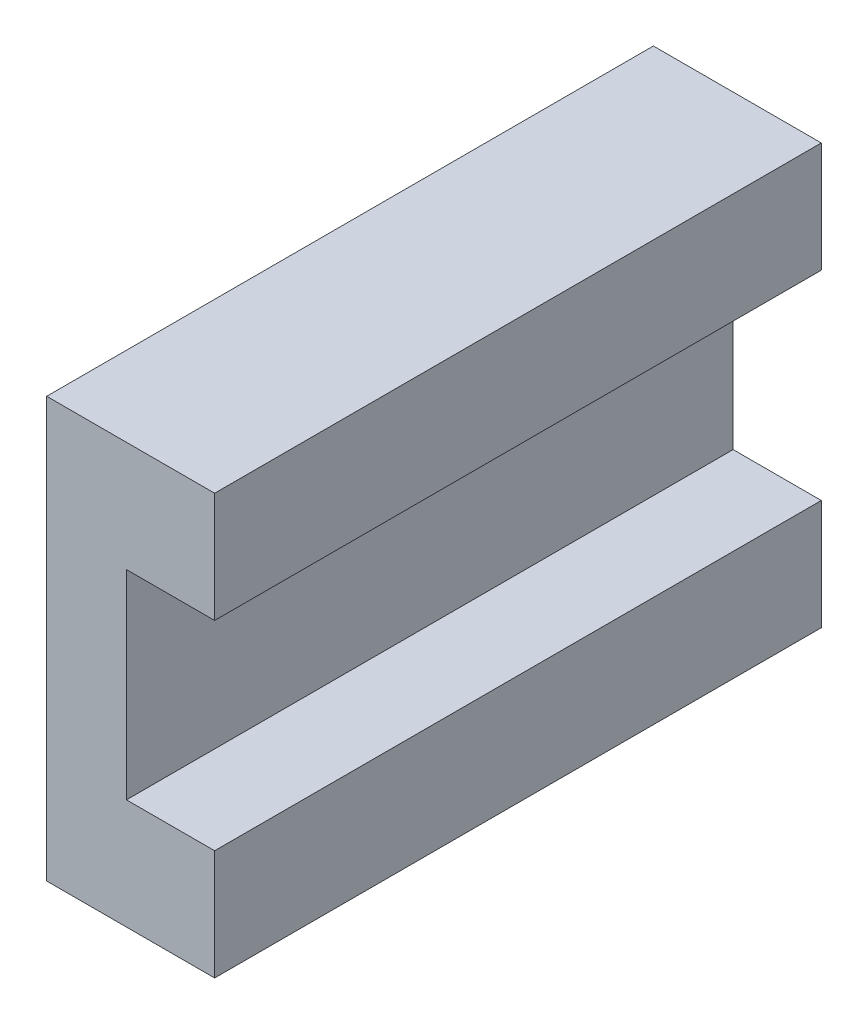
SolidWorks part; units mm, degrees
ref_plane "Front Plane" through (0, 0, 0) normal (0, 0, 1) x (1, 0, 0)
ref_plane "Top Plane" through (0, 0, 0) normal (0, 1, 0) x (1, 0, 0)
ref_plane "Right Plane" through (0, 0, 0) normal (1, 0, 0) x (0, 0, -1)
sketch "Sketch1" plane through (0, 0, 0) normal (0, 0, 1) x (1, 0, 0)
  line L1 (3.25, 4.5) -> (-3.25, 4.5)
  line L2 (3.25, 4.5) -> (3.25, -4.5)
  line L3 (3.25, -4.5) -> (-3.25, -4.5)
  line L4 (-3.25, 4.5) -> (-3.25, -4.5)
  line L5 (0, -4.5) -> (0, 4.5) construction
  line L6 (3.25, 0) -> (-3.25, 0) construction
  point P0 (0, 0)
  dimension "D1" = 6.5
  dimension "D2" = 9
extrude "Boss-Extrude1" add sketch "Sketch1" along normal mid plane 300
sketch "Sketch2" plane through (0, 0, 0) normal (0, 0, 1) x (1, 0, 0)
  line L0 (3.25, -4.5) -> (3.25, 4.5) construction
  line L1 (0.75, 10) -> (-7.25, 10)
  line L2 (0.75, 10) -> (0.75, -10)
  line L3 (0.75, -10) -> (-7.25, -10)
  line L4 (-7.25, 10) -> (-7.25, -10)
  line L5 (-3.25, -10) -> (-3.25, 10) construction
  line L6 (0.75, 0) -> (-7.25, 0) construction
  line L7 (0.75, 4.75) -> (-3.45, 4.75)
  line L8 (0.75, 4.75) -> (0.75, -4.75)
  line L9 (0.75, -4.75) -> (-3.45, -4.75)
  line L10 (-3.45, 4.75) -> (-3.45, -4.75)
  line L11 (-1.35, -4.75) -> (-1.35, 4.75) construction
  line L12 (0.75, 0) -> (-3.45, 0) construction
  line L13 (-3.25, 4.5) -> (-3.25, -4.5) construction
  point P144 (-1.35, 0)
  point P340 (-3.25, 0)
  dimension "D1" = 8
  dimension "D2" = 2.5
  dimension "D3" = 0.2
  dimension "D4" = 9.5
  dimension "D5" = 20
extrude "Boss-Extrude2" add sketch "Sketch2" along normal mid plane 28.9 separate body contours L10 L7 L2 L1 L4 L3 L9
hole_wizard "M3x0.5 Tapped Hole1" positions "Sketch3" profile "Sketch4" tap size "M3x0.5" standard "ANSI Metric"
sketch "Sketch3" plane through (-7.25, 0, 0) normal (-1, 0, 0) x (0, 0, 1)
  line L1 (-5, 7.5) -> (5, 7.5)
  line L2 (-5, 7.5) -> (-5, -7.5)
  line L3 (-5, -7.5) -> (5, -7.5)
  line L4 (5, 7.5) -> (5, -7.5)
  line L5 (0, -7.5) -> (0, 7.5) construction
  line L6 (-5, 0) -> (5, 0) construction
  point P5 (-5, 7.5)
  point P6 (5, -7.5)
  point P259 (-5, -7.5)
  point P260 (5, 7.5)
  dimension "D1" = 10
  dimension "D2" = 15
sketch "Sketch4" plane through (-7.25, 7.5, -5) normal (0, 1, 0) x (0, 0, 1)
  line L0 (0, 0) -> (0, 3.7511)
  line L1 (0, 3.7511) -> (1.25, 3)
  line L2 (1.25, 3) -> (1.25, 0)
  line L5 (1.25, 0) -> (0, 0)
  line L10 (0, 3.7511) -> (-1.25, 3) construction
  line L11 (0, -6.35) -> (0, 107.95) construction
  dimension "Tap Drill Dia." = 2.5
  dimension "Tap Drill Depth" = 3
  dimension "Drill Angle" = 118
hole_wizard "CBORE for M3 SHCS1" positions "Sketch5" profile "Sketch6" counterbore size "M3" standard "ANSI Metric" end condition through all
sketch "Sketch5" plane through (-3.25, 0, 0) normal (-1, 0, 0) x (0, 0, 1)
  line L0 (-150, 0) -> (-140, 0) construction
  line L1 (-150, 4.5) -> (-150, -4.5) construction
  point P0 (-140, 0)
  dimension "D1" = 10
sketch "Sketch6" plane through (-3.25, 0, -140) normal (0, 1, 0) x (0, 0, 1)
  line L0 (0, 0) -> (0, 6.5)
  line L1 (0, 6.5) -> (1.8, 6.5)
  line L3 (1.8, 6.5) -> (1.8, 3)
  line L4 (1.8, 3) -> (3.25, 3)
  line L5 (3.25, 3) -> (3.25, 0)
  line L7 (3.25, 0) -> (0, 0)
  line L11 (0, -6.35) -> (0, 107.95) construction
  dimension "Thru Hole Dia." = 3.6
  dimension "Thru Hole Depth" = 6.5
  dimension "C'Bore Dia." = 6.5
  dimension "C'Bore Depth" = 3
pattern_linear "LPattern1" count 15 spacing 20 along (0, 0, 1) of "CBORE for M3 SHCS1"
move or copy body "Body-Move/Copy1" bodies to move or copy 103 copy no translate (0, 0, 5)
delete or keep bodies "Body-Delete/Keep 1" type delete bodies bodies 105
